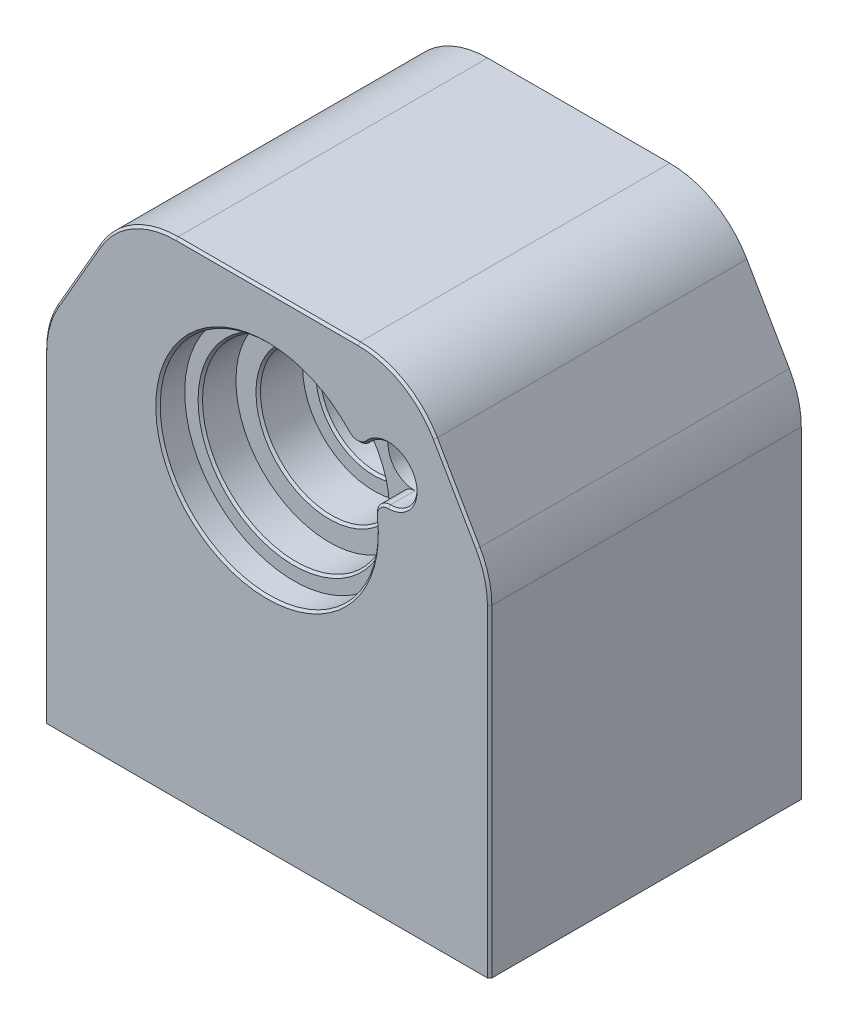
SolidWorks part; units mm, degrees
material "Alumine"
ref_plane "Plan de face" through (0, 0, 0) normal (0, 0, 1) x (1, 0, 0)
ref_plane "Plan de dessus" through (0, 0, 0) normal (0, 1, 0) x (1, 0, 0)
ref_plane "Plan de droite" through (0, 0, 0) normal (1, 0, 0) x (0, 0, -1)
sketch "Esquisse1" plane through (0, 0, 0) normal (0, 0, 1) x (1, 0, 0)
  line L0 (-32, 35) -> (-50, 3.8231)
  line L1 (-50, -35) -> (50, -35) construction
  line L2 (-50, -35) -> (-50, 35)
  line L3 (-50, 35) -> (50, 35)
  line L4 (50, -35) -> (50, 35)
  line L5 (-50, -35) -> (50, 35) construction
  line L6 (-50, 35) -> (50, -35) construction
  line L7 (32, 35) -> (50, 3.8231)
  line L9 (-50, -35) -> (50, -35)
  line L10 (-50, -35) -> (-50, -74)
  line L11 (-50, -74) -> (50, -74)
  line L12 (50, -35) -> (50, -74)
  point P0 (0, 0)
  dimension "D1" = 70
  dimension "D2" = 100
  dimension "D3" = 150
  dimension "D4" = 150
  dimension "D5" = 18
  dimension "D6" = 18
  dimension "D7" = 39
extrude "Boss.-Extru.1" add sketch "Esquisse1" along normal blind 70 contours L1 L4 L3 L2 | L10 L9 L12 L11
hole_wizard "Trou pour taraudage pour trou taraudé M121" positions "Esquisse3" profile "Esquisse4" hole size "M12" standard "ISO" end condition through all
sketch "Esquisse3" plane through (0, -30, 0) normal (0, 0, 1) x (-1, 0, 0)
  line L2 (-27.1892, -42.6785) -> (0, -30) construction
  line L5 (32, -65) -> (-32, -65) construction
  point P0 (-27.1892, -42.6785)
  point P7 (0, -30)
  dimension "D1" = 30
  dimension "D2" = 155
sketch "Esquisse4" plane through (27.1892, 12.6785, 0) normal (1, 0, 0) x (0, 1, 0)
  line L0 (0, 0) -> (0, 70)
  line L1 (0, 70) -> (5.1, 70)
  line L2 (5.1, 70) -> (5.1, 0)
  line L5 (5.1, 0) -> (0, 0)
  line L11 (0, -6.35) -> (0, 107.95) construction
  dimension "Diamètre du perçage jusqu'au prochain" = 10.2
  dimension "Profondeur du perçage jusqu'au prochain" = 70
hole_wizard "Dégagement M121" positions "Esquisse6" profile "Esquisse7" hole size "M12" standard "ISO"
sketch "Esquisse6" plane through (0, 30, 0) normal (0, 0, 1) x (1, 0, 0)
  point P0 (27.1892, -17.3215)
sketch "Esquisse7" plane through (27.1892, 12.6785, 0) normal (1, 0, 0) x (0, 1, 0)
  line L0 (0, 0) -> (0, 44.0558)
  line L1 (0, 44.0558) -> (6.75, 40)
  line L2 (6.75, 40) -> (6.75, 0)
  line L5 (6.75, 0) -> (0, 0)
  line L10 (0, 44.0558) -> (-6.75, 40) construction
  line L11 (0, -6.35) -> (0, 107.95) construction
  dimension "Diamètre du perçage" = 13.5
  dimension "Profondeur du perçage" = 40
  dimension "Angle de pointe" = 118
fillet "Congé2" radius 20 4 edges at (-50, 3.8231, 35) (50, 3.8231, 35) (-32, 35, 35) (32, 35, 35)
sketch "Esquisse8" plane through (0, -74, 0) normal (0, -1, 0) x (1, 0, 0)
  line L0 (-50, 70) -> (-50, 0) construction
  line L1 (-50, 70) -> (50, 70) construction
  circle A0 centre (-18, 29) radius 10
  dimension "D1" = 20
  dimension "D3" = 41
  dimension "D2" = 32
extrude "Enlèv. mat.-Extru.2" cut sketch "Esquisse8" against normal offset from surface (89 mm away) 20 up to face at (0, 35, 35)
sketch "Esquisse9" plane through (0, -74, 0) normal (0, -1, 0) x (1, 0, 0)
  line L0 (-50, 0) -> (50, 0) construction
  line L2 (-46.5, 0.5) -> (-46.5, 57.5)
  line L3 (-46.5, 57.5) -> (10.5, 57.5)
  line L4 (10.5, 0.5) -> (10.5, 57.5)
  line L5 (-46.5, 0.5) -> (10.5, 57.5) construction
  line L6 (-46.5, 57.5) -> (10.5, 0.5) construction
  line L8 (-46.5, 0.5) -> (-46.5, 0)
  line L9 (-46.5, 0) -> (10.5, 0)
  line L10 (10.5, 0.5) -> (10.5, 0)
  line L11 (38, 56.7) -> (38, 45)
  line L14 (25, 56.7) -> (28, 56.7) construction
  line L17 (28, 66.7) -> (20, 66.7)
  line L18 (-50, 70) -> (50, 70) construction
  line L19 (50, 70) -> (50, 0) construction
  line L21 (10, 56.7) -> (10, 45)
  line L22 (10, 45) -> (38, 45)
  arc A2 (38, 56.7) -> (28, 66.7) centre (28, 56.7) ccw
  arc A3 (20, 66.7) -> (10, 56.7) centre (20, 56.7) ccw
  point P0 (-18, 29)
  point P14 (27.5, 57.2582)
  dimension "D2" = 45
  dimension "D6" = 10
  dimension "D7" = 10
  dimension "D1" = 57
  dimension "D3" = 12
  dimension "D4" = 3.3
  dimension "D5" = 25
  dimension "D8" = 8
extrude "Enlèv. mat.-Extru.3" cut sketch "Esquisse9" against normal blind 49
fillet "Congé3" radius 4 1 edges at (-46.5, -49.5, 57.5)
sketch "Esquisse10" plane through (0, -25, 0) normal (0, -1, 0) x (1, 0, 0)
  circle A0 centre (-18, 29) radius 20
  dimension "D1" = 40
extrude "Enlèv. mat.-Extru.4" cut sketch "Esquisse10" against normal blind 2
hole_wizard "Trou pour taraudage pour trou taraudé M51" positions "Esquisse11" profile "Esquisse12" hole size "M5" standard "ISO"
sketch "Esquisse11" plane through (0, -25, 0) normal (0, -1, 0) x (-1, 0, 0)
  line L1 (41.57, -5.43) -> (-5.57, -5.43) construction
  line L2 (41.57, -5.43) -> (41.57, -52.57) construction
  line L3 (41.57, -52.57) -> (-5.57, -52.57) construction
  line L4 (-5.57, -5.43) -> (-5.57, -52.57) construction
  line L5 (41.57, -5.43) -> (-5.57, -52.57) construction
  line L6 (41.57, -52.57) -> (-5.57, -5.43) construction
  point P1 (-5.57, -52.57)
  point P64 (41.57, -5.43)
  point P65 (41.57, -52.57)
  point P66 (-5.57, -5.43)
  point P81 (18, -29)
  dimension "D1" = 47.14
sketch "Esquisse12" plane through (5.57, -25, 52.57) normal (1, 0, 0) x (0, 0, -1)
  line L0 (0, 0) -> (0, 9.2618)
  line L1 (0, 9.2618) -> (2.1, 8)
  line L2 (2.1, 8) -> (2.1, 0)
  line L5 (2.1, 0) -> (0, 0)
  line L10 (0, 9.2618) -> (-2.1, 8) construction
  line L11 (0, -6.35) -> (0, 107.95) construction
  dimension "Diamètre du perçage" = 4.2
  dimension "Profondeur du perçage" = 8
  dimension "Angle de pointe" = 118
sketch "Esquisse14" plane through (0, 0, 0) normal (1, 0, 0) x (0, 0, -1)
  line L0 (0, 0) -> (-70, 0)
  line L1 (-70, 25) -> (-70, 8.4641) construction
  line L2 (-70, 24.5) -> (-64, 24.5)
  line L3 (-64, 24.5) -> (-64, 21)
  line L4 (-64, 21) -> (-56, 21)
  line L5 (-56, 21) -> (-56, 16)
  line L6 (-56, 16) -> (-46, 16)
  line L7 (-46, 16) -> (-46, 12.5)
  line L8 (-46, 12.5) -> (-14.9987, 12.5)
  line L9 (-14.9987, 12.5) -> (-14.9987, 14)
  line L10 (-14.9987, 14) -> (0.0013, 14)
  line L11 (-70, 24.5) -> (-70, 0)
  line L12 (0.0013, 14) -> (0, 0)
  line L13 (0, 0) -> (-70, 0) construction
  dimension "D1" = 24.5
  dimension "D2" = 21
  dimension "D3" = 15
  dimension "D4" = 12.5
  dimension "D5" = 14
  dimension "D6" = 16
  dimension "D7" = 10
  dimension "D8" = 8
  dimension "D9" = 6
revolve "Enlèvement de matière-Révolution2" cut sketch "Esquisse14" angle 360 about L0
sketch "Esquisse15" plane through (0, 0, 70) normal (0, 0, 1) x (1, 0, 0)
  circle A0 centre (27.1892, 12.6785) radius 6
  dimension "D1" = 12
extrude "Enlèv. mat.-Extru.5" cut sketch "Esquisse15" against normal blind 15
fillet "Congé4" radius 3 2 edges at (23.0326, 8.3516, 67) (21.2028, 12.2757, 67)
sketch "Esquisse16" plane through (0, 0, 0) normal (0, 0, -1) x (-1, 0, 0)
  line L0 (-10.5, -74) -> (-50, -74) construction
  line L3 (-38, -74) -> (-20.4392, -74)
  line L4 (-19.1892, 12.6785) -> (-19.1892, -25)
  line L5 (-38, -74) -> (-38, 9.9538)
  line L6 (-38, 9.9538) -> (-34.1174, 16.6785)
  line L10 (-10.5, -74) -> (-20.4392, -74)
  line L11 (-10.5, -74) -> (-10.5, -25)
  line L12 (-10.5, -25) -> (-19.1892, -25)
  line L13 (-50, -74) -> (-50, -1.5359) construction
  arc A2 (-19.1892, 12.6785) -> (-34.1174, 16.6785) centre (-27.1892, 12.6785) ccw
  dimension "D1" = 16
  dimension "D2" = 12
extrude "Enlèv. mat.-Extru.6" cut sketch "Esquisse16" against normal blind 45
fillet "Congé5" radius 20 1 edges at (38, 9.9538, 22.5)
fillet "Congé6" radius 6 1 edges at (19.1892, -25, 22.5)
hole_wizard "Trou pour taraudage pour trou taraudé M52" positions "Esquisse17" profile "Esquisse18" hole size "M5" standard "ISO"
sketch "Esquisse17" plane through (0, -74, 0) normal (0, -1, 0) x (-1, 0, 0)
  line L0 (50, -70) -> (-50, -70) construction
  line L1 (-50, -70) -> (-50, 0) construction
  line L2 (-38, 0) -> (-50, 0) construction
  line L3 (50, -70) -> (50, 0) construction
  point P0 (44, -64)
  point P2 (-44, -64)
  point P4 (-44, -15)
  dimension "D1" = 6
  dimension "D2" = 6
  dimension "D3" = 15
  dimension "D4" = 6
sketch "Esquisse18" plane through (-44, -74, 64) normal (1, 0, 0) x (0, 0, -1)
  line L0 (0, 0) -> (0, 31.2618)
  line L1 (0, 31.2618) -> (2.1, 30)
  line L2 (2.1, 30) -> (2.1, 0)
  line L5 (2.1, 0) -> (0, 0)
  line L10 (0, 31.2618) -> (-2.1, 30) construction
  line L11 (0, -6.35) -> (0, 107.95) construction
  dimension "Diamètre du perçage" = 4.2
  dimension "Profondeur du perçage" = 30
  dimension "Angle de pointe" = 118
hole_wizard "Trou pour taraudage pour trou taraudé M41" positions "Esquisse19" profile "Esquisse20" hole size "M4" standard "ISO"
sketch "Esquisse19" plane through (0, 0, 0) normal (0, 0, -1) x (-1, 0, 0)
  line L1 (-50, -74) -> (-50, -1.5359) construction
  line L2 (-37.7735, 25) -> (-47.3205, 8.4641) construction
  line L3 (37.7735, 25) -> (47.3205, 8.4641) construction
  line L4 (50, -74) -> (50, -1.5359) construction
  line L5 (20.453, 35) -> (-20.453, 35) construction
  line L6 (-38, -74) -> (-50, -74) construction
  line L7 (-10.0321, -74) -> (42.5, -74) construction
  point P0 (44, -14)
  point P2 (30.8453, 25)
  point P4 (-30.8453, 25)
  point P6 (-44, -68)
  dimension "D1" = 6
  dimension "D2" = 6
  dimension "D3" = 6
  dimension "D4" = 6
  dimension "D5" = 10
  dimension "D6" = 6
  dimension "D7" = 60
sketch "Esquisse20" plane through (-44, -14, 0) normal (1, 0, 0) x (0, 1, 0)
  line L0 (0, 0) -> (0, 8.9914)
  line L1 (0, 8.9914) -> (1.65, 8)
  line L2 (1.65, 8) -> (1.65, 0)
  line L5 (1.65, 0) -> (0, 0)
  line L10 (0, 8.9914) -> (-1.65, 8) construction
  line L11 (0, -6.35) -> (0, 107.95) construction
  dimension "Diamètre du perçage" = 3.3
  dimension "Profondeur du perçage" = 8
  dimension "Angle de pointe" = 118
chamfer "Chanfrein2" distance 0.5 angle 45 18 edges at (-12.5, 0, 46) (-16, 0, 56) (32.6271, 15.2143, 70) (24.9871, 5.6451, 70) (20.3858, 15.5126, 70) (-22.2045, -10.3541, 70) (-21, 0, 64) (-12.5, 0, 14.9987) (14, 0, 0) (-50, -37.7679, 70) (-49.3185, 3.6405, 70) (-42.547, 16.7321, 70) (-30.453, 32.3205, 70) (0, 35, 70) (30.453, 32.3205, 70) (42.547, 16.7321, 70) (49.3185, 3.6405, 70) (50, -37.7679, 70)
fillet "Congé7" radius 6 1 edges at (10.0321, -49.5, 57.5)
